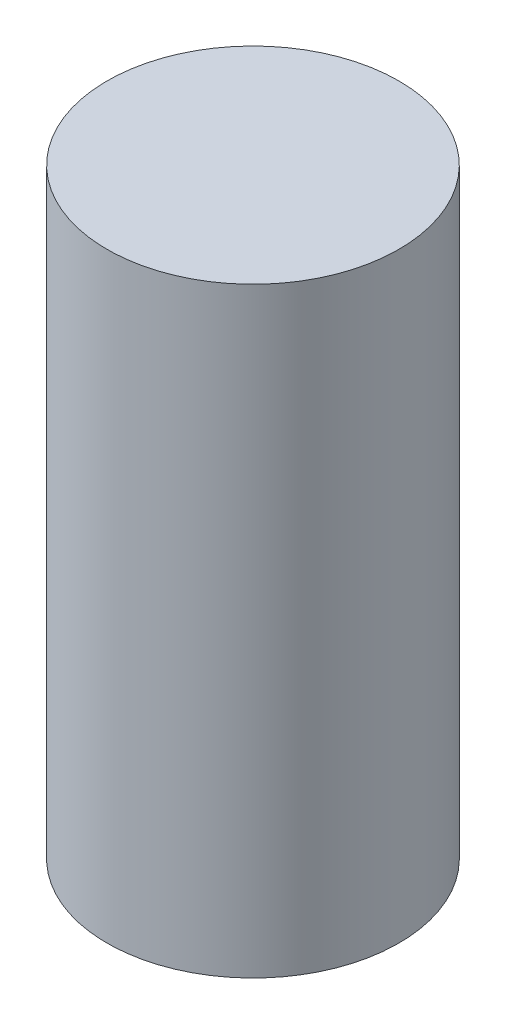
SolidWorks part; units mm, degrees
ref_plane "Front Plane" through (0, 0, 0) normal (0, 0, 1) x (1, 0, 0)
ref_plane "Top Plane" through (0, 0, 0) normal (0, 1, 0) x (1, 0, 0)
ref_plane "Right Plane" through (0, 0, 0) normal (1, 0, 0) x (0, 0, -1)
sketch "Sketch1" plane through (0, 0, 0) normal (0, 0, 1) x (1, 0, 0)
  line L0 (0, 0) -> (0.762, 0)
  line L1 (0.762, 0) -> (0.762, 8.89)
  line L2 (0.762, 8.89) -> (-1.397, 8.89)
  line L3 (-1.397, 8.89) -> (-1.397, 5.08)
  line L4 (-1.397, 5.08) -> (0, 5.08)
  line L5 (0, 5.08) -> (0, 0)
  line L6 (-1.397, 0.1505) -> (-1.397, 10.636) construction
  dimension "D1" = 2.159
  dimension "D2" = 1.397
  dimension "D3" = 8.89
  dimension "D4" = 5.08
revolve "Revolve1" add sketch "Sketch1" angle 360 about L6
